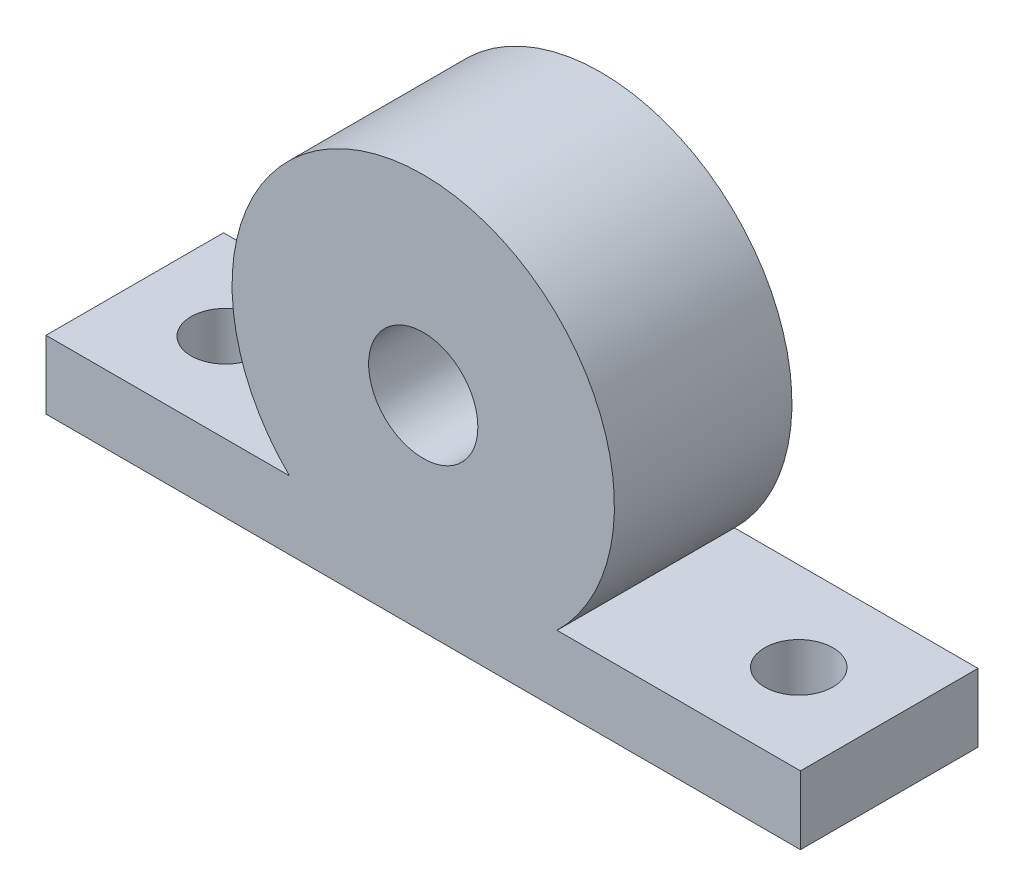
SolidWorks part; units mm, degrees
ref_plane "Front Plane" through (0, 0, 0) normal (0, 0, 1) x (1, 0, 0)
ref_plane "Top Plane" through (0, 0, 0) normal (0, 1, 0) x (1, 0, 0)
ref_plane "Right Plane" through (0, 0, 0) normal (1, 0, 0) x (0, 0, -1)
sketch "Sketch1" plane through (0, 0, 0) normal (0, 0, 1) x (1, 0, 0)
  line L0 (-27.625, -15) -> (27.625, -15)
  line L1 (0, 0) -> (0, -30) construction
  line L2 (-27.625, -15) -> (-27.625, -10)
  line L3 (-27.625, -10) -> (-9.798, -10)
  line L4 (27.625, -10) -> (27.625, -15)
  line L5 (9.798, -10) -> (27.625, -10)
  circle A0 centre (0, 0) radius 4
  arc A1 (9.798, -10) -> (-9.798, -10) centre (0, 0) ccw
  point P5 (0, -15)
  dimension "D1" = 8
  dimension "D3" = 15
  dimension "D4" = 28
  dimension "D2" = 55.25
  dimension "D5" = 5
extrude "Boss-Extrude1" add sketch "Sketch1" along normal blind 13
sketch "Sketch2" plane through (0, -15, 0) normal (0, -1, 0) x (1, 0, 0)
  line L0 (-27.625, 6.5) -> (27.625, 6.5) construction
  line L1 (-27.625, 13) -> (-27.625, 0) construction
  line L2 (27.625, 13) -> (27.625, 0) construction
  circle A0 centre (-21, 6.5) radius 2.5
  circle A1 centre (21, 6.5) radius 2.5
  point P10 (0, 6.5)
  dimension "D1" = 5
  dimension "D2" = 5
  dimension "D3" = 21
  dimension "D4" = 21
extrude "Cut-Extrude1" cut sketch "Sketch2" against normal through all
